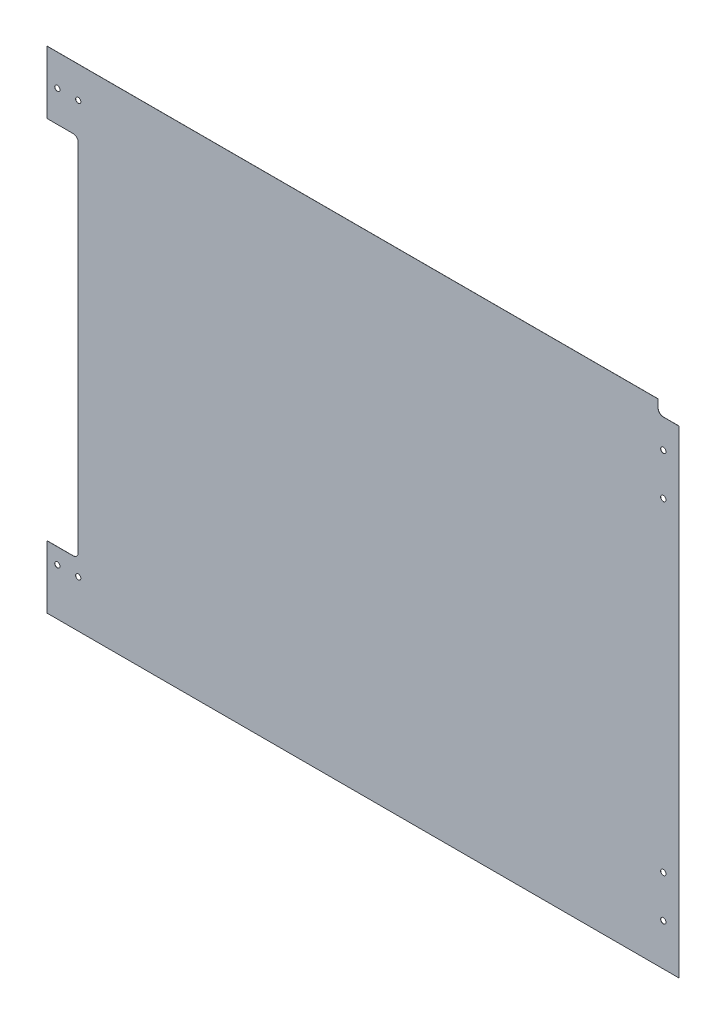
SolidWorks part; units mm, degrees
material "PC High Viscosity"
ref_plane "Front Plane" through (0, 0, 0) normal (0, 0, 1) x (1, 0, 0)
ref_plane "Top Plane" through (0, 0, 0) normal (0, 1, 0) x (1, 0, 0)
ref_plane "Right Plane" through (0, 0, 0) normal (1, 0, 0) x (0, 0, -1)
sketch "Sketch1" plane through (0, 0, 0) normal (0, 0, 1) x (1, 0, 0)
  line L1 (-368.3, -298.45) -> (368.3, -298.45)
  line L2 (-368.3, -298.45) -> (-368.3, 298.45)
  line L3 (-368.3, 298.45) -> (368.3, 298.45)
  line L4 (368.3, -298.45) -> (368.3, 298.45)
  line L5 (-368.3, -298.45) -> (368.3, 298.45) construction
  line L6 (-368.3, 298.45) -> (368.3, -298.45) construction
  point P0 (0, 0)
  dimension "D1" = 596.9
  dimension "D2" = 736.6
extrude "Boss-Extrude1" add sketch "Sketch1" along normal blind 0.127
sketch "Sketch2" plane through (0, 0, 0.127) normal (0, 0, 1) x (1, 0, 0)
  line L0 (-368.3, 285.75) -> (368.3, 285.75) construction
  line L1 (-368.3, 298.45) -> (-368.3, -298.45) construction
  line L2 (368.3, -298.45) -> (368.3, 298.45) construction
  line L3 (-368.3, 0) -> (368.3, 0) construction
  line L4 (368.3, 298.45) -> (-368.3, 298.45) construction
  line L5 (-368.3, -285.75) -> (368.3, -285.75) construction
  line L6 (-355.6, 298.45) -> (-355.6, -298.45) construction
  line L7 (-368.3, -298.45) -> (368.3, -298.45) construction
  line L8 (0, 298.45) -> (0, -298.45) construction
  point P8 (-336.55, 285.75)
  point P9 (336.55, 285.75)
  point P15 (336.55, -285.75)
  point P16 (-336.55, -285.75)
  point P23 (-355.6, 250.825)
  point P24 (355.6, 250.825)
  point P25 (355.6, -250.825)
  point P26 (-355.6, -250.825)
  dimension "D1" = 12.7
  dimension "D2" = 31.75
  dimension "D3" = 31.75
  dimension "D4" = 12.7
  dimension "D5" = 47.625
hole_wizard "1/4 (0.25) Diameter Hole1" positions "Sketch3" profile "Sketch4" hole size "1/4" standard "ANSI Inch"
sketch "Sketch3" plane through (0, 0, 6.35) normal (0, 0, 1) x (1, 0, 0)
  point P0 (-336.55, 290.5125)
  point P3 (336.55, 290.5125)
  point P16 (-355.6, 255.5875)
  point P20 (355.6, 255.5875)
  point P24 (-355.6, -255.5875)
  point P27 (355.6, -255.5875)
  point P30 (336.55, -290.5125)
  point P33 (-336.55, -290.5125)
sketch "Sketch4" plane through (-336.55, 290.5125, 6.35) normal (1, 0, 0) x (0, -1, 0)
  line L0 (0, 0) -> (0, 6.35)
  line L1 (0, 6.35) -> (3.175, 6.35)
  line L2 (3.175, 6.35) -> (3.175, 0)
  line L5 (3.175, 0) -> (0, 0)
  line L11 (0, -6.35) -> (0, 107.95) construction
  dimension "Thru Hole Dia." = 6.35
  dimension "Thru Hole Depth" = 6.35
sketch "Sketch5" plane through (0, 0, 0.127) normal (0, 0, 1) x (1, 0, 0)
  line L1 (-368.3, 298.45) -> (-400.05, 298.45)
  line L2 (-368.3, 298.45) -> (-368.3, 222.25)
  line L3 (-368.3, 222.25) -> (-400.05, 222.25)
  line L4 (-400.05, 298.45) -> (-400.05, 222.25)
  line L5 (-368.3, -298.45) -> (-400.05, -298.45)
  line L6 (-368.3, -298.45) -> (-368.3, -222.25)
  line L7 (-368.3, -222.25) -> (-400.05, -222.25)
  line L8 (-400.05, -298.45) -> (-400.05, -222.25)
  dimension "D1" = 31.75
  dimension "D2" = 76.2
  dimension "D3" = 76.2
extrude "Boss-Extrude2" add sketch "Sketch5" against normal up to surface (0.127 mm away) up to face at (0, 0, 0)
sketch "Sketch6" plane through (0, 0, 0.127) normal (0, 0, 1) x (1, 0, 0)
  line L0 (-368.3, -222.25) -> (-400.05, -222.25) construction
  line L1 (-368.3, 222.25) -> (-361.95, 222.25)
  line L2 (-368.3, 222.25) -> (-368.3, -222.25)
  line L3 (-368.3, -222.25) -> (-361.95, -222.25)
  line L4 (-361.95, 222.25) -> (-361.95, -222.25)
  dimension "D1" = 6.35
extrude "Cut-Extrude1" cut sketch "Sketch6" against normal through all
fillet "Fillet1" radius 6.35 2 edges at (-361.95, 222.25, 0.0635) (-361.95, -222.25, 0.0635)
sketch "Sketch7" plane through (0, 0, 0.127) normal (0, 0, 1) x (1, 0, 0)
  line L0 (349.25, 298.45) -> (349.25, -298.45) construction
  line L1 (368.3, 298.45) -> (-400.05, 298.45) construction
  line L2 (-400.05, -298.45) -> (368.3, -298.45) construction
  line L3 (368.3, -298.45) -> (368.3, 298.45) construction
  line L4 (349.25, 0) -> (-361.95, 0) construction
  line L5 (-361.95, -215.9) -> (-361.95, 215.9) construction
  point P8 (349.25, 247.65)
  point P9 (349.25, 196.85)
  point P14 (349.25, -247.65)
  point P15 (349.25, -196.85)
  dimension "D1" = 19.05
  dimension "D2" = 50.8
  dimension "D3" = 50.8
hole_wizard "F (0.257) Diameter Hole1" positions "Sketch8" profile "Sketch9" hole size "F" standard "ANSI Inch" end condition through all
sketch "Sketch8" plane through (0, 0, 0.127) normal (0, 0, 1) x (1, 0, 0)
  point P0 (349.25, 247.65)
  point P3 (349.25, 196.85)
  point P6 (349.25, -196.85)
  point P9 (349.25, -247.65)
sketch "Sketch9" plane through (349.25, 247.65, 0.127) normal (1, 0, 0) x (0, -1, 0)
  line L0 (0, 0) -> (0, 0.127)
  line L1 (0, 0.127) -> (3.2639, 0.127)
  line L2 (3.2639, 0.127) -> (3.2639, 0)
  line L5 (3.2639, 0) -> (0, 0)
  line L11 (0, -6.35) -> (0, 107.95) construction
  dimension "Thru Hole Dia." = 6.5278
  dimension "Thru Hole Depth" = 0.127
sketch "Sketch10" plane through (0, 0, 0.127) normal (0, 0, 1) x (1, 0, 0)
  line L0 (-400.05, 260.35) -> (-361.95, 260.35) construction
  line L1 (-400.05, 298.45) -> (-400.05, 222.25) construction
  line L2 (-361.95, 0) -> (349.25, 0) construction
  line L3 (349.25, 298.45) -> (349.25, -298.45) construction
  line L4 (-400.05, -241.3) -> (-361.95, -241.3) construction
  line L6 (-400.05, -298.45) -> (368.3, -298.45) construction
  line L7 (-400.05, -222.25) -> (-400.05, -298.45) construction
  point P4 (-387.35, 260.35)
  point P6 (-361.95, 260.35)
  point P13 (-387.35, -241.3)
  dimension "D1" = 12.7
  dimension "D2" = 38.1
  dimension "D3" = 57.15
  dimension "D4" = 12.7
  dimension "D5" = 38.1
hole_wizard "1/4 (0.25) Diameter Hole2" positions "Sketch11" profile "Sketch12" hole size "1/4" standard "ANSI Inch"
sketch "Sketch11" plane through (0, 0, 0.127) normal (0, 0, 1) x (1, 0, 0)
  point P0 (-387.35, 260.35)
  point P3 (-361.95, 260.35)
  point P6 (-361.95, -241.3)
  point P9 (-387.35, -241.3)
sketch "Sketch12" plane through (-387.35, 260.35, 0.127) normal (1, 0, 0) x (0, -1, 0)
  line L0 (0, 0) -> (0, 2.0337)
  line L1 (0, 2.0337) -> (3.175, 0.126)
  line L2 (3.175, 0.126) -> (3.175, 0)
  line L5 (3.175, 0) -> (0, 0)
  line L10 (0, 2.0337) -> (-3.175, 0.126) construction
  line L11 (0, -6.35) -> (0, 107.95) construction
  dimension "Hole Dia." = 6.35
  dimension "Hole Depth" = 0.126
  dimension "Drill Angle" = 118
sketch "Sketch13" plane through (0, 0, 0.127) normal (0, 0, 1) x (1, 0, 0)
  line L1 (368.3, 298.45) -> (342.9, 298.45)
  line L2 (368.3, 298.45) -> (368.3, 282.575)
  line L3 (368.3, 282.575) -> (349.25, 282.575)
  line L4 (342.9, 298.45) -> (342.9, 288.925)
  arc A0 (349.25, 282.575) -> (342.9, 288.925) centre (349.25, 288.925) cw
  point P7 (342.9, 282.575)
  dimension "D3" = 6.35
  dimension "D1" = 25.4
  dimension "D2" = 15.875
extrude "Cut-Extrude2" cut sketch "Sketch13" against normal through all
equation "\"D3@Sketch2\"=\"D2@Sketch2\""
